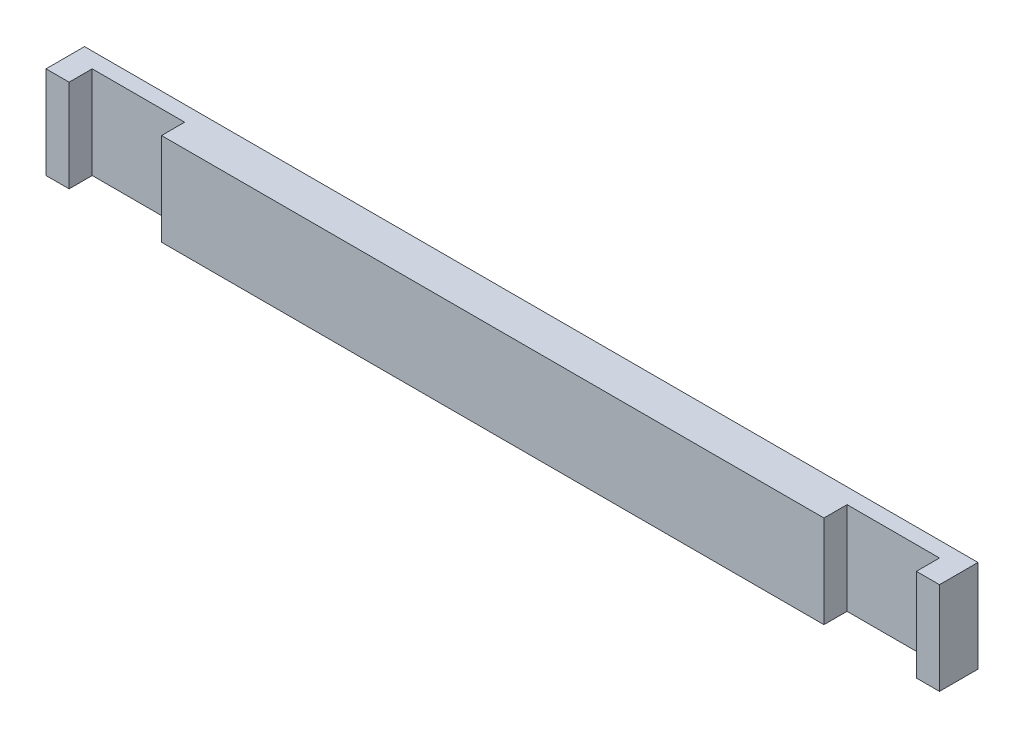
SolidWorks part; units mm, degrees
ref_plane "Спереди" through (0, 0, 0) normal (0, 0, 1) x (1, 0, 0)
ref_plane "Сверху" through (0, 0, 0) normal (0, 1, 0) x (1, 0, 0)
ref_plane "Справа" through (0, 0, 0) normal (1, 0, 0) x (0, 0, -1)
sketch "Эскиз1" plane through (0, 0, 0) normal (0, 1, 0) x (1, 0, 0)
  line L0 (215, 0) -> (-215, 0)
  line L5 (-215, 0) -> (-215, 15)
  line L6 (-215, 15) -> (-275, 15)
  line L7 (-275, 15) -> (-275, 0)
  line L8 (-275, 0) -> (-290, 0)
  line L9 (-290, 0) -> (-290, 25)
  line L10 (-290, 25) -> (290, 25)
  line L11 (0, 22.2095) -> (0, -15.1214) construction
  line L12 (290, 0) -> (290, 25)
  line L13 (275, 0) -> (290, 0)
  line L14 (275, 15) -> (275, 0)
  line L15 (215, 15) -> (275, 15)
  line L16 (215, 0) -> (215, 15)
  point P0 (0, 0)
  point P3 (0, 0)
  point P16 (0, 25)
  point P21 (0, 0)
extrude "Бобышка-Вытянуть1" add sketch "Эскиз1" along normal blind 60
